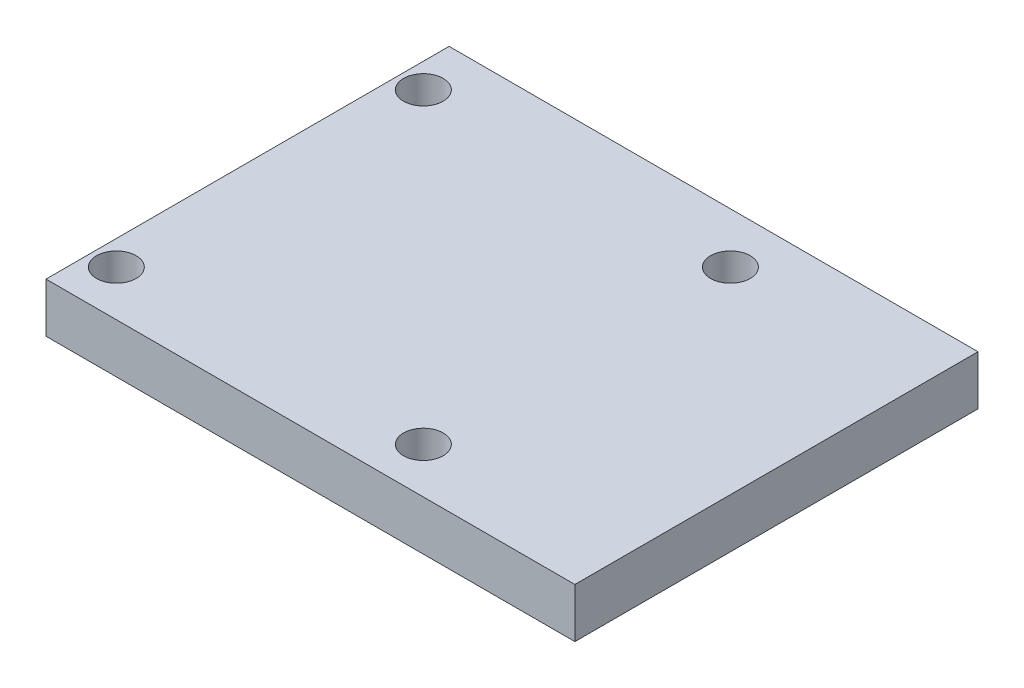
SolidWorks part; units mm, degrees
ref_plane "Front Plane" through (0, 0, 0) normal (0, 0, 1) x (1, 0, 0)
ref_plane "Top Plane" through (0, 0, 0) normal (0, 1, 0) x (1, 0, 0)
ref_plane "Right Plane" through (0, 0, 0) normal (1, 0, 0) x (0, 0, -1)
sketch "Sketch1" plane through (0, 0, 0) normal (0, 1, 0) x (1, 0, 0)
  line L1 (-26.7, -20.35) -> (26.7, -20.35)
  line L2 (-26.7, -20.35) -> (-26.7, 20.35)
  line L3 (-26.7, 20.35) -> (26.7, 20.35)
  line L4 (26.7, -20.35) -> (26.7, 20.35)
  line L5 (-26.7, -20.35) -> (26.7, 20.35) construction
  line L6 (-26.7, 20.35) -> (26.7, -20.35) construction
  point P0 (0, 0)
  dimension "D1" = 53.4
  dimension "D2" = 40.7
extrude "Boss-Extrude1" add sketch "Sketch1" along normal blind 5
sketch "Sketch2" plane through (0, 5, 0) normal (0, 1, 0) x (1, 0, 0)
  line L0 (-26.7, 20.35) -> (-26.7, -20.35) construction
  line L1 (26.7, 20.35) -> (-26.7, 20.35) construction
  circle A0 centre (-24.2, 15.25) radius 2
  circle A1 centre (-24.2, -15.75) radius 2
  circle A2 centre (6.8, 15.25) radius 2
  circle A3 centre (6.8, -15.75) radius 2
  dimension "D1" = 4
  dimension "D4" = 4
  dimension "D5" = 4
  dimension "D6" = 4
  dimension "D2" = 2.5
  dimension "D3" = 5.1
  dimension "D7" = 31
  dimension "D8" = 31
  dimension "D9" = 0
  dimension "D10" = 0
  dimension "D11" = 5.1
  dimension "D12" = 31
extrude "Cut-Extrude1" cut sketch "Sketch2" against normal blind 5
